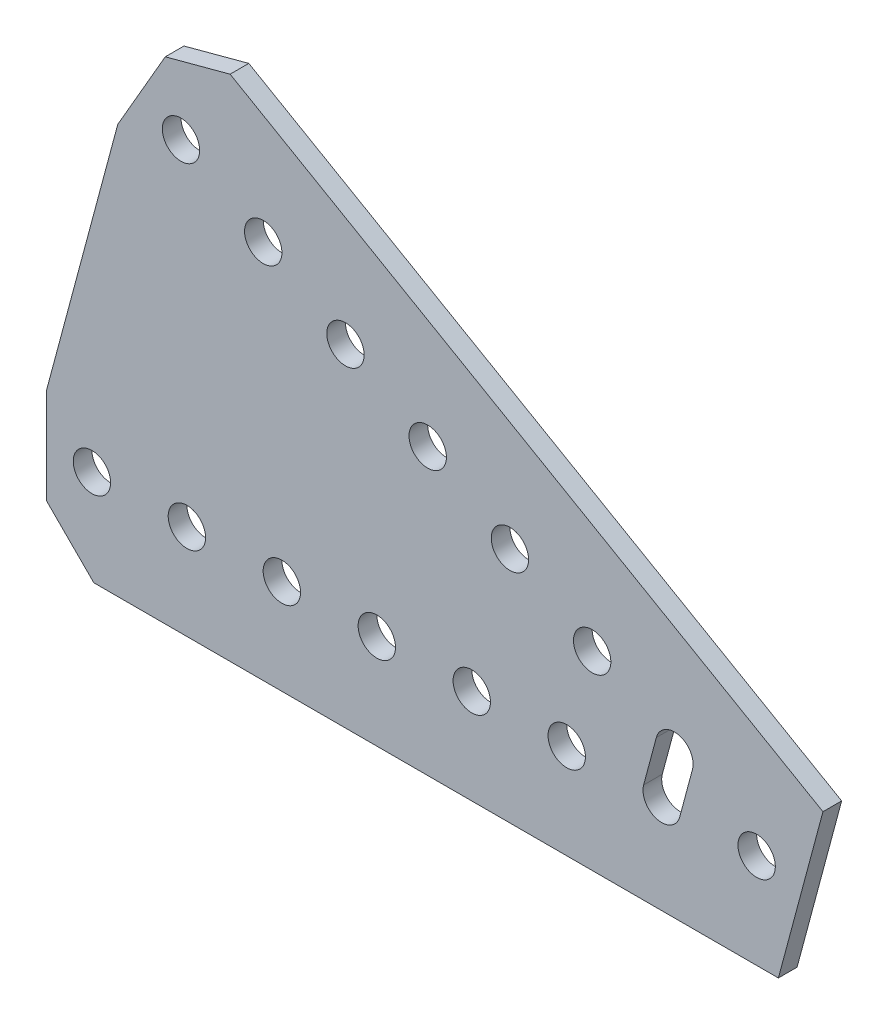
SolidWorks part; units mm, degrees
material "5052-H32"
ref_plane "Front Plane" through (0, 0, 0) normal (0, 0, 1) x (1, 0, 0)
ref_plane "Top Plane" through (0, 0, 0) normal (0, 1, 0) x (1, 0, 0)
ref_plane "Right Plane" through (0, 0, 0) normal (1, 0, 0) x (0, 0, -1)
ref_plane "Plane1" through (0, 0, -1.25) normal (0, 0, -1) x (-1, 0, 0)
sketch "Sketch1" plane through (0, 0, -1.25) normal (0, 0, -1) x (-1, 0, 0)
  line L0 (10.2852, -0.647) -> (8.5837, 5.703)
  line L1 (13.4133, 6.997) -> (15.1148, 0.647)
  line L2 (-2.9081, -12.7) -> (88.646, -12.7)
  line L3 (88.646, -12.7) -> (94.996, -6.35)
  line L4 (94.996, -6.35) -> (94.996, 6.35)
  line L5 (94.996, 6.35) -> (85.4439, 41.9987)
  line L6 (85.4439, 41.9987) -> (79.0939, 52.9973)
  line L7 (79.0939, 52.9973) -> (70.4197, 55.3215)
  line L8 (70.4197, 55.3215) -> (-8.8685, 9.5445)
  line L9 (-8.8685, 9.5445) -> (-2.9081, -12.7)
  circle A0 centre (25.4, 0) radius 2.5
  circle A1 centre (38.1, 0) radius 2.5
  circle A2 centre (50.8, 0) radius 2.5
  circle A3 centre (63.5, 0) radius 2.5
  circle A4 centre (0, 0) radius 2.5
  circle A5 centre (88.9, 0) radius 2.5
  circle A6 centre (76.2, 0) radius 2.5
  circle A7 centre (76.9897, 44.45) radius 2.5
  circle A8 centre (65.9911, 38.1) radius 2.5
  circle A9 centre (54.9926, 31.75) radius 2.5
  circle A10 centre (43.9941, 25.4) radius 2.5
  circle A11 centre (32.9956, 19.05) radius 2.5
  circle A12 centre (21.997, 12.7) radius 2.5
  arc A13 (15.1148, 0.647) -> (10.2852, -0.647) centre (12.7, 0) cw
  arc A14 (8.5837, 5.703) -> (13.4133, 6.997) centre (10.9985, 6.35) cw
extrude "Boss-Extrude1" add sketch "Sketch1" against normal blind 2.5
